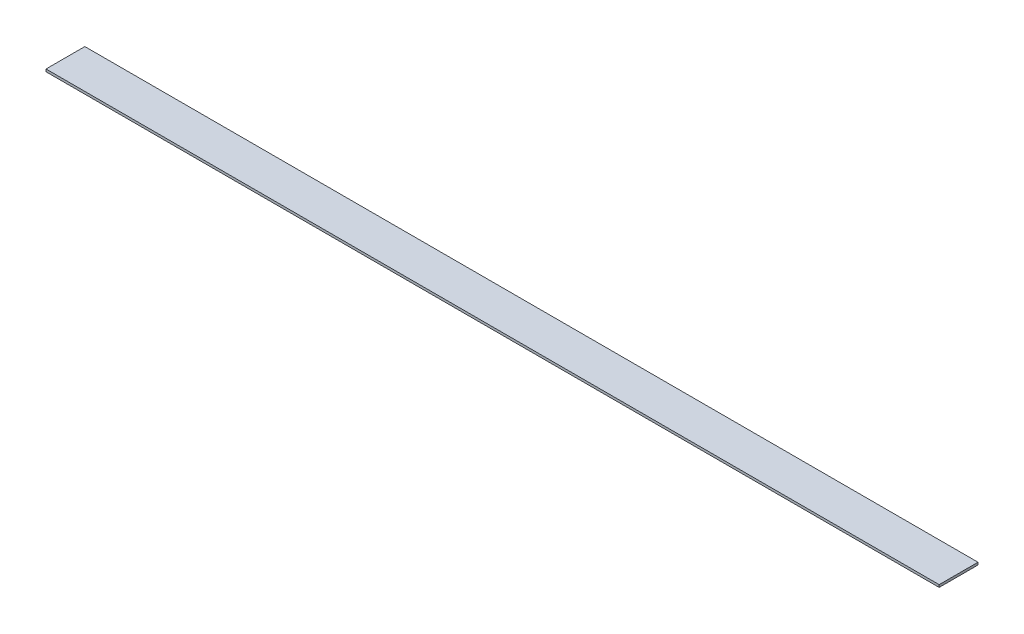
SolidWorks part; units mm, degrees
material "Very Low Density PE (SS)"
ref_plane "Front Plane" through (0, 0, 0) normal (0, 0, 1) x (1, 0, 0)
ref_plane "Top Plane" through (0, 0, 0) normal (0, 1, 0) x (1, 0, 0)
ref_plane "Right Plane" through (0, 0, 0) normal (1, 0, 0) x (0, 0, -1)
sketch "Sketch1" plane through (0, 0, 0) normal (0, 1, 0) x (1, 0, 0)
  line L1 (584.2, -25.4) -> (-584.2, -25.4)
  line L2 (584.2, -25.4) -> (584.2, 25.4)
  line L3 (584.2, 25.4) -> (-584.2, 25.4)
  line L4 (-584.2, -25.4) -> (-584.2, 25.4)
  line L5 (584.2, -25.4) -> (-584.2, 25.4) construction
  line L6 (584.2, 25.4) -> (-584.2, -25.4) construction
  point P0 (0, 0)
  dimension "D1" = 1168.4
  dimension "D2" = 50.8
extrude "Boss-Extrude1" add sketch "Sketch1" along normal blind 3.175
